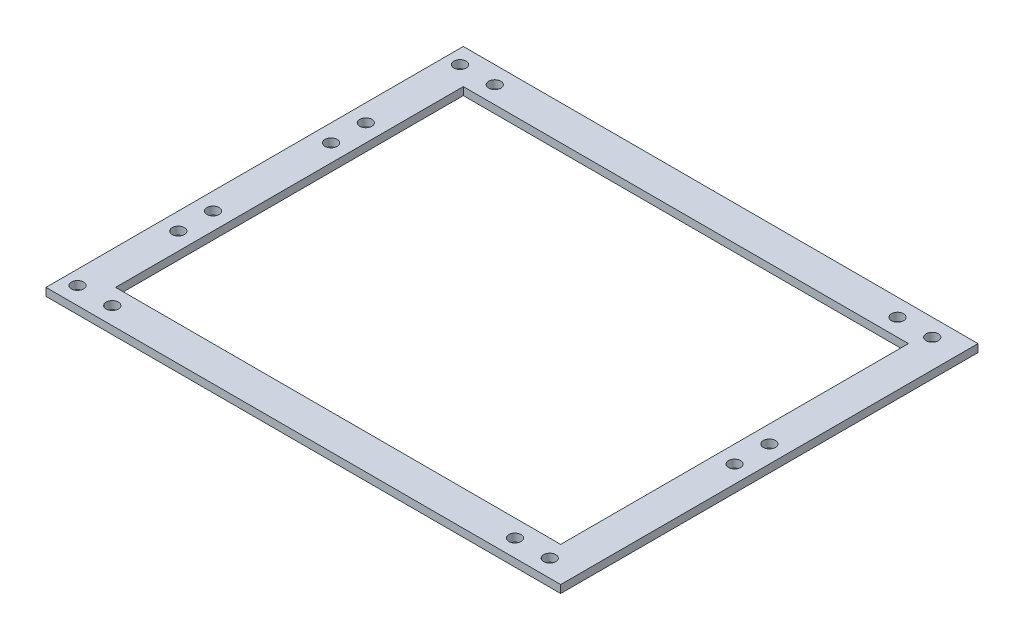
SolidWorks part; units mm, degrees
ref_plane "Front Plane" through (0, 0, 0) normal (0, 0, 1) x (1, 0, 0)
ref_plane "Top Plane" through (0, 0, 0) normal (0, 1, 0) x (1, 0, 0)
ref_plane "Right Plane" through (0, 0, 0) normal (1, 0, 0) x (0, 0, -1)
sketch "Sketch1" plane through (0, 0, 0) normal (0, 1, 0) x (1, 0, 0)
  line L1 (-148, -120) -> (148, -120)
  line L2 (-148, -120) -> (-148, 120)
  line L3 (-148, 120) -> (148, 120)
  line L4 (148, -120) -> (148, 120)
  line L5 (-148, -120) -> (148, 120) construction
  line L6 (-148, 120) -> (148, -120) construction
  line L7 (-128, 100) -> (128, 100)
  line L8 (-128, 100) -> (-128, -100)
  line L9 (-128, -100) -> (128, -100)
  line L10 (128, 100) -> (128, -100)
  point P0 (0, 0)
  dimension "D1" = 296
  dimension "D2" = 240
  dimension "D3" = 20
  dimension "D4" = 20
  dimension "D5" = 20
  dimension "D6" = 20
extrude "Boss-Extrude1" add sketch "Sketch1" along normal blind 4.5
sketch "Sketch2" plane through (0, 4.5, 0) normal (0, 1, 0) x (1, 0, 0)
  line L0 (-148, -110) -> (-139.9, -110)
  line L1 (-148, 120) -> (-148, -120) construction
  line L2 (-139.9, -110) -> (-119.9, -110)
  circle A0 centre (-139.9, -110) radius 3.5
  circle A1 centre (-119.9, -110) radius 3.5
  dimension "D4" = 7
  dimension "D5" = 7
  dimension "D1" = 10
  dimension "D2" = 8.1
  dimension "D3" = 20
extrude "Cut-Extrude1" cut sketch "Sketch2" against normal blind 4.5
mirror "Mirror1" about plane through (0, 0, 0) normal (0, 0, 1) of "Cut-Extrude1"
sketch "Sketch3" plane through (0, 4.5, 0) normal (0, 1, 0) x (1, 0, 0)
  line L0 (148, -110) -> (131.7, -110)
  line L1 (148, -120) -> (148, 120) construction
  line L2 (131.7, -110) -> (111.7, -110)
  circle A0 centre (131.7, -110) radius 3.5
  circle A1 centre (111.7, -110) radius 3.5
  dimension "D4" = 7
  dimension "D5" = 7
  dimension "D1" = 10
  dimension "D2" = 16.3
  dimension "D3" = 20
extrude "Cut-Extrude2" cut sketch "Sketch3" against normal blind 4.5
mirror "Mirror2" about plane through (0, 0, 0) normal (0, 0, 1) of "Cut-Extrude2"
sketch "Sketch4" plane through (0, 4.5, 0) normal (0, 1, 0) x (1, 0, 0)
  line L0 (138, 10) -> (138, -10)
  line L1 (138, 0) -> (148, 0)
  line L2 (148, -120) -> (148, 120) construction
  circle A0 centre (138, 10) radius 3.5
  circle A1 centre (138, -10) radius 3.5
  dimension "D3" = 7
  dimension "D4" = 7
  dimension "D1" = 10
  dimension "D2" = 20
extrude "Cut-Extrude3" cut sketch "Sketch4" against normal blind 4.5
sketch "Sketch5" plane through (0, 4.5, 0) normal (0, 1, 0) x (1, 0, 0)
  line L0 (-238.5131, 53.924) -> (-148, 53.924)
  line L1 (-148, 120) -> (-148, -120) construction
  line L2 (-148, 53.924) -> (-138, 53.924)
  line L3 (-138, 53.924) -> (-138, 33.924)
  line L4 (-238.5131, -53.924) -> (-148, -53.924)
  line L5 (-148, -53.924) -> (-138, -53.924)
  line L6 (-138, -53.924) -> (-138, -33.924)
  circle A0 centre (-242.0131, 53.924) radius 3.5 construction
  circle A1 centre (-242.0131, -53.924) radius 3.5 construction
  circle A2 centre (-138, 53.924) radius 3.5
  circle A3 centre (-138, 33.924) radius 3.5
  circle A4 centre (-138, -33.924) radius 3.5
  circle A5 centre (-138, -53.924) radius 3.5
  dimension "D2" = 7
  dimension "D3" = 7
  dimension "D4" = 7
  dimension "D5" = 7
  dimension "D1" = 10
  dimension "D6" = 10
  dimension "D7" = 20
  dimension "D8" = 20
extrude "Cut-Extrude4" cut sketch "Sketch5" against normal blind 4.5
